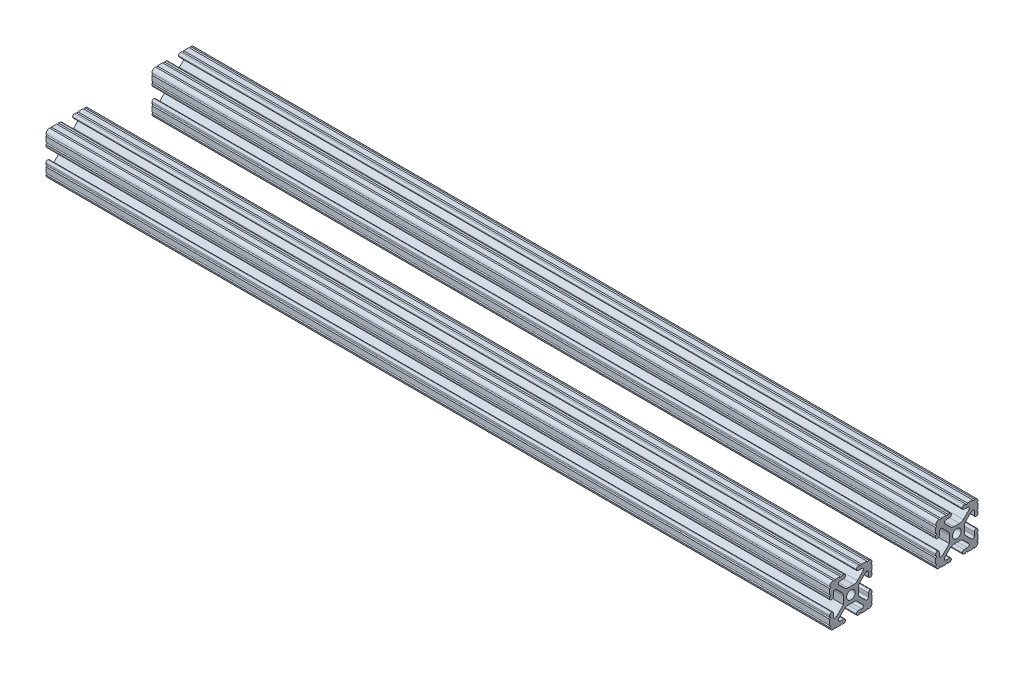
SolidWorks part; units mm, degrees
material "6061-T6 (SS)"
material "6061-T6 (SS)"
material "6061-T6 (SS)"
ref_plane "Front Plane" through (0, 0, 0) normal (0, 0, 1) x (1, 0, 0)
ref_plane "Top Plane" through (0, 0, 0) normal (0, 1, 0) x (1, 0, 0)
ref_plane "Right Plane" through (0, 0, 0) normal (1, 0, 0) x (0, 0, -1)
sketch3d "3DSketch2"
  line L0 (0, 0, 0) -> (-469.9, 0, 0)
  line L1 (0, 0, -63.5) -> (-469.9, 0, -63.5)
  dimension "D1" = 63.5
  dimension "D2" = 469.9
other "8020 10 series 1 X 1 X .25(2)"
ref_plane "Plane2" through (0, 0, 0) normal (-1, 0, 0) x (0, 0, 1)
sketch "Sketch1" plane through (0, 0, 0) normal (-1, 0, 0) x (0, 0, 1)
  line L0 (6.3331, -12.7) -> (9.5504, -12.7)
  line L1 (12.7, -9.5504) -> (12.7, -6.3331)
  line L2 (12.7, -5.3171) -> (12.7, -4.2875)
  line L3 (11.651, -3.2385) -> (11.5392, -3.2385)
  line L4 (10.4902, -4.2875) -> (10.4902, -6.4021)
  line L5 (8.7371, -7.1294) -> (4.5085, -2.9104)
  line L6 (4.5085, -2.9104) -> (4.5085, 1.5932)
  line L7 (5.441, 3.8408) -> (8.7371, 7.1294)
  line L8 (10.4902, 6.4021) -> (10.4902, 4.2875)
  line L9 (11.5392, 3.2385) -> (11.651, 3.2385)
  line L10 (12.7, 4.2875) -> (12.7, 5.3171)
  line L11 (12.7, 6.3331) -> (12.7, 9.5504)
  line L12 (9.5504, 12.7) -> (6.3331, 12.7)
  line L13 (5.3171, 12.7) -> (4.2875, 12.7)
  line L14 (3.2385, 11.651) -> (3.2385, 11.5392)
  line L15 (4.2875, 10.4902) -> (6.4768, 10.4902)
  line L16 (7.207, 8.7244) -> (3.8983, 5.4232)
  line L17 (1.6558, 4.4958) -> (-1.6558, 4.4958)
  line L18 (-3.8983, 5.4232) -> (-7.207, 8.7244)
  line L19 (-6.4768, 10.4902) -> (-4.2875, 10.4902)
  line L20 (-3.2385, 11.5392) -> (-3.2385, 11.651)
  line L21 (-4.2875, 12.7) -> (-5.3171, 12.7)
  line L22 (-6.3331, 12.7) -> (-9.5504, 12.7)
  line L23 (-12.7, 9.5504) -> (-12.7, 6.3331)
  line L24 (-12.7, 5.3171) -> (-12.7, 4.2875)
  line L25 (-11.651, 3.2385) -> (-11.5392, 3.2385)
  line L26 (-10.4902, 4.2875) -> (-10.4902, 6.4021)
  line L27 (-8.7371, 7.1294) -> (-5.441, 3.8408)
  line L28 (-4.5085, 1.5932) -> (-4.5085, -1.5932)
  line L29 (-5.441, -3.8408) -> (-8.7371, -7.1294)
  line L30 (-10.4902, -6.4021) -> (-10.4902, -4.2875)
  line L31 (-11.5392, -3.2385) -> (-11.651, -3.2385)
  line L32 (-12.7, -4.2875) -> (-12.7, -5.3171)
  line L33 (-12.7, -6.3331) -> (-12.7, -9.5504)
  line L34 (-9.5504, -12.7) -> (-6.3331, -12.7)
  line L35 (-5.3171, -12.7) -> (-4.2875, -12.7)
  line L36 (-3.2385, -11.651) -> (-3.2385, -11.5392)
  line L37 (-4.2875, -10.4902) -> (-6.4164, -10.4902)
  line L38 (-7.1797, -8.6452) -> (-3.9523, -5.4237)
  line L39 (-1.7093, -4.4958) -> (1.7093, -4.4958)
  line L40 (3.9523, -5.4237) -> (7.1797, -8.6452)
  line L41 (6.4164, -10.4902) -> (4.2875, -10.4902)
  line L42 (3.2385, -11.5392) -> (3.2385, -11.651)
  line L43 (4.2875, -12.7) -> (5.3171, -12.7)
  circle A0 centre (0, 0) radius 2.6035
  arc A1 (6.3331, -12.7) -> (5.3171, -12.7) centre (5.8251, -12.7) ccw
  arc A2 (10.5664, -12.6998) -> (9.5504, -12.7) centre (10.0584, -12.7) ccw
  arc A3 (10.5664, -12.6998) -> (12.6998, -10.5664) centre (10.5918, -10.5918) ccw
  arc A4 (12.7, -9.5504) -> (12.6998, -10.5664) centre (12.7, -10.0584) ccw
  arc A5 (12.7, -5.3171) -> (12.7, -6.3331) centre (12.7, -5.8251) ccw
  arc A6 (12.7, -4.2875) -> (11.651, -3.2385) centre (11.651, -4.2875) ccw
  arc A7 (11.5392, -3.2385) -> (10.4902, -4.2875) centre (11.5392, -4.2875) ccw
  arc A8 (8.7371, -7.1294) -> (10.4902, -6.4021) centre (9.4628, -6.4021) ccw
  arc A9 (5.441, 3.8408) -> (4.5085, 1.5932) centre (7.6835, 1.5932) ccw
  arc A10 (10.4902, 6.4021) -> (8.7371, 7.1294) centre (9.4628, 6.4021) ccw
  arc A11 (10.4902, 4.2875) -> (11.5392, 3.2385) centre (11.5392, 4.2875) ccw
  arc A12 (11.651, 3.2385) -> (12.7, 4.2875) centre (11.651, 4.2875) ccw
  arc A13 (12.7, 6.3331) -> (12.7, 5.3171) centre (12.7, 5.8251) ccw
  arc A14 (12.6998, 10.5664) -> (12.7, 9.5504) centre (12.7, 10.0584) ccw
  arc A15 (12.6998, 10.5664) -> (10.5664, 12.6998) centre (10.5918, 10.5918) ccw
  arc A16 (9.5504, 12.7) -> (10.5664, 12.6998) centre (10.0584, 12.7) ccw
  arc A17 (5.3171, 12.7) -> (6.3331, 12.7) centre (5.8251, 12.7) ccw
  arc A18 (4.2875, 12.7) -> (3.2385, 11.651) centre (4.2875, 11.651) ccw
  arc A19 (3.2385, 11.5392) -> (4.2875, 10.4902) centre (4.2875, 11.5392) ccw
  arc A20 (7.207, 8.7244) -> (6.4768, 10.4902) centre (6.4768, 9.4563) ccw
  arc A21 (1.6558, 4.4958) -> (3.8983, 5.4232) centre (1.6558, 7.6708) ccw
  arc A22 (-3.8983, 5.4232) -> (-1.6558, 4.4958) centre (-1.6558, 7.6708) ccw
  arc A23 (-6.4768, 10.4902) -> (-7.207, 8.7244) centre (-6.4768, 9.4563) ccw
  arc A24 (-4.2875, 10.4902) -> (-3.2385, 11.5392) centre (-4.2875, 11.5392) ccw
  arc A25 (-3.2385, 11.651) -> (-4.2875, 12.7) centre (-4.2875, 11.651) ccw
  arc A26 (-6.3331, 12.7) -> (-5.3171, 12.7) centre (-5.8251, 12.7) ccw
  arc A27 (-10.5664, 12.6998) -> (-9.5504, 12.7) centre (-10.0584, 12.7) ccw
  arc A28 (-10.5664, 12.6998) -> (-12.6998, 10.5664) centre (-10.5918, 10.5918) ccw
  arc A29 (-12.7, 9.5504) -> (-12.6998, 10.5664) centre (-12.7, 10.0584) ccw
  arc A30 (-12.7, 5.3171) -> (-12.7, 6.3331) centre (-12.7, 5.8251) ccw
  arc A31 (-12.7, 4.2875) -> (-11.651, 3.2385) centre (-11.651, 4.2875) ccw
  arc A32 (-11.5392, 3.2385) -> (-10.4902, 4.2875) centre (-11.5392, 4.2875) ccw
  arc A33 (-8.7371, 7.1294) -> (-10.4902, 6.4021) centre (-9.4628, 6.4021) ccw
  arc A34 (-4.5085, 1.5932) -> (-5.441, 3.8408) centre (-7.6835, 1.5932) ccw
  arc A35 (-5.441, -3.8408) -> (-4.5085, -1.5932) centre (-7.6835, -1.5932) ccw
  arc A36 (-10.4902, -6.4021) -> (-8.7371, -7.1294) centre (-9.4628, -6.4021) ccw
  arc A37 (-10.4902, -4.2875) -> (-11.5392, -3.2385) centre (-11.5392, -4.2875) ccw
  arc A38 (-11.651, -3.2385) -> (-12.7, -4.2875) centre (-11.651, -4.2875) ccw
  arc A39 (-12.7, -6.3331) -> (-12.7, -5.3171) centre (-12.7, -5.8251) ccw
  arc A40 (-12.6998, -10.5664) -> (-12.7, -9.5504) centre (-12.7, -10.0584) ccw
  arc A41 (-12.6998, -10.5664) -> (-10.5664, -12.6998) centre (-10.5918, -10.5918) ccw
  arc A42 (-9.5504, -12.7) -> (-10.5664, -12.6998) centre (-10.0584, -12.7) ccw
  arc A43 (-5.3171, -12.7) -> (-6.3331, -12.7) centre (-5.8251, -12.7) ccw
  arc A44 (-4.2875, -12.7) -> (-3.2385, -11.651) centre (-4.2875, -11.651) ccw
  arc A45 (-3.2385, -11.5392) -> (-4.2875, -10.4902) centre (-4.2875, -11.5392) ccw
  arc A46 (-7.1797, -8.6452) -> (-6.4164, -10.4902) centre (-6.4164, -9.4098) ccw
  arc A47 (-1.7093, -4.4958) -> (-3.9523, -5.4237) centre (-1.7093, -7.6708) ccw
  arc A48 (3.9523, -5.4237) -> (1.7093, -4.4958) centre (1.7093, -7.6708) ccw
  arc A49 (6.4164, -10.4902) -> (7.1797, -8.6452) centre (6.4164, -9.4098) ccw
  arc A50 (4.2875, -10.4902) -> (3.2385, -11.5392) centre (4.2875, -11.5392) ccw
  arc A51 (3.2385, -11.651) -> (4.2875, -12.7) centre (4.2875, -11.651) ccw
  point P148 (0, 0)
